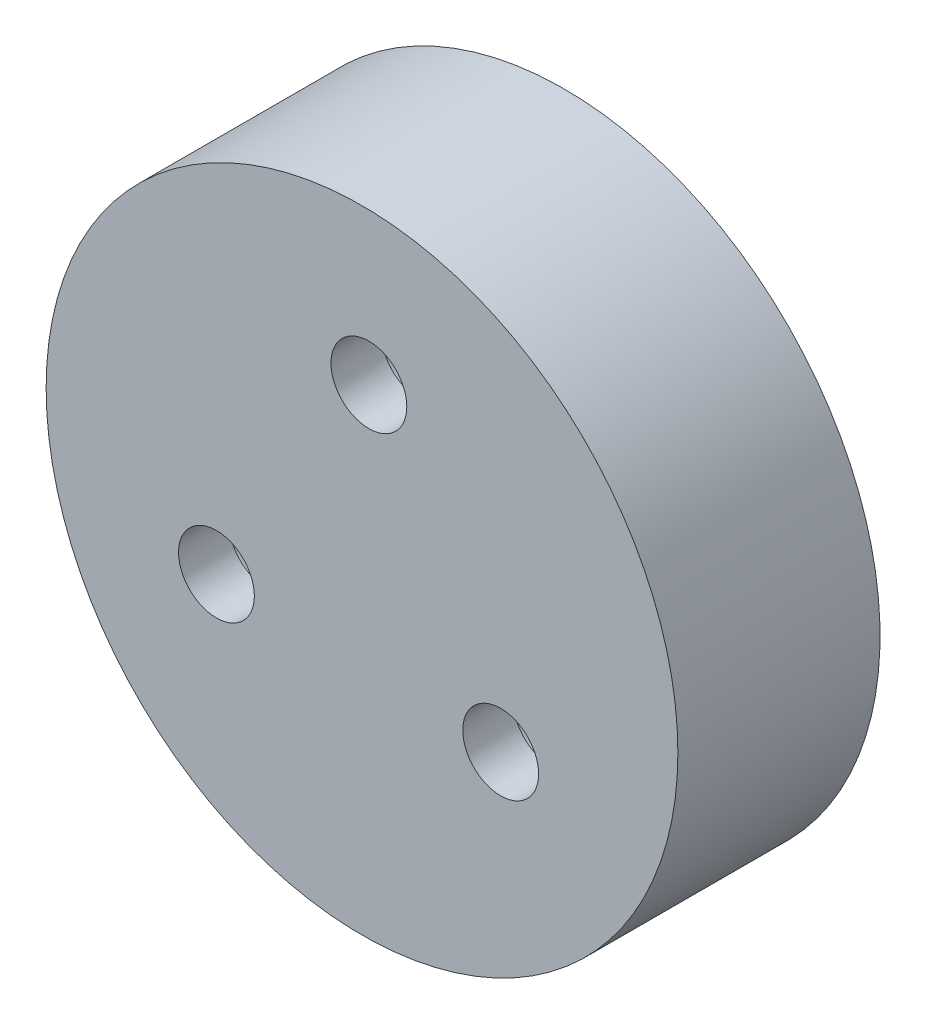
SolidWorks part; units mm, degrees
ref_plane "Front Plane" through (0, 0, 0) normal (0, 0, 1) x (1, 0, 0)
ref_plane "Top Plane" through (0, 0, 0) normal (0, 1, 0) x (1, 0, 0)
ref_plane "Right Plane" through (0, 0, 0) normal (1, 0, 0) x (0, 0, -1)
sketch "Sketch2" plane through (0, 0, 0) normal (0, 0, 1) x (1, 0, 0)
  circle A0 centre (0, 0) radius 12.5
  dimension "D1" = 25
extrude "Boss-Extrude1" add sketch "Sketch2" along normal blind 6
hole_wizard "1/4-20 Tapped Hole1" [suppressed] positions "Sketch3" profile "Sketch5" tap size "1/4-20" standard "ANSI Inch"
sketch "Sketch3" plane through (0, 0, 12) normal (0, 0, 1) x (1, 0, 0)
  point P0 (0, 0)
sketch "Sketch5" plane through (0, 0, 12) normal (1, 0, 0) x (0, -1, 0)
  line L0 (0, 0) -> (0, 7.5338)
  line L1 (0, 7.5338) -> (2.5527, 6)
  line L2 (2.5527, 6) -> (2.5527, 0)
  line L5 (2.5527, 0) -> (0, 0)
  line L10 (0, 7.5338) -> (-2.5527, 6) construction
  line L11 (0, -6.35) -> (0, 107.95) construction
  dimension "Tap Drill Dia." = 5.1054
  dimension "Tap Drill Depth" = 6
  dimension "Drill Angle" = 118
cosmetic thread "Hole Thread1" [suppressed] parameters "D1"=12.7, "D2"=6.35
sketch "Sketch6" plane through (0, 0, 0) normal (0, 0, -1) x (-1, 0, 0)
  line L1 (-5.4882, -3.4828) -> (5.7603, -3.0115) construction
  line L2 (5.7603, -3.0115) -> (-0.2721, 6.4943) construction
  line L3 (-0.2721, 6.4943) -> (-5.4882, -3.4828) construction
  circle A0 centre (0, 0) radius 3.25
  circle A1 centre (-5.4882, -3.4828) radius 1.5
  circle A2 centre (-0.2721, 6.4943) radius 1.5
  circle A3 centre (5.7603, -3.0115) radius 1.5
  dimension "D2" = 3
  dimension "D3" = 3
  dimension "D4" = 3
  dimension "D1" = 6.5
extrude "Cut-Extrude1" cut sketch "Sketch6" against normal blind 15 contours A2 | A1 | A3
sketch "Sketch7" plane through (0, 0, 6) normal (0, 0, 1) x (1, 0, 0)
  circle A0 centre (-5.7603, -3.0115) radius 2
  circle A1 centre (0.2721, 6.4943) radius 2
  circle A2 centre (5.4882, -3.4828) radius 2
  dimension "D1" = 4
  dimension "D2" = 4
  dimension "D3" = 4
extrude "Cut-Extrude2" [suppressed] cut sketch "Sketch7" against normal blind 10
sketch "Sketch8" plane through (0, 0, 0) normal (0, 0, -1) x (-1, 0, 0)
  circle A0 centre (0, 0) radius 10
  circle A1 centre (0, 0) radius 12.5 construction
  circle A2 centre (0, 0) radius 12.5
  dimension "D1" = 20
extrude "Boss-Extrude2" add sketch "Sketch8" along normal blind 2
sketch "Sketch9" plane through (0, 0, 0) normal (0, 0, -1) x (-1, 0, 0)
  circle A0 centre (-0.2721, 6.4943) radius 2.5
  circle A1 centre (5.7603, -3.0115) radius 2.5
  circle A2 centre (-5.4882, -3.4828) radius 2.5
  dimension "D1" = 5
  dimension "D2" = 5
  dimension "D3" = 5
extrude "Cut-Extrude3" cut sketch "Sketch9" against normal blind 4
